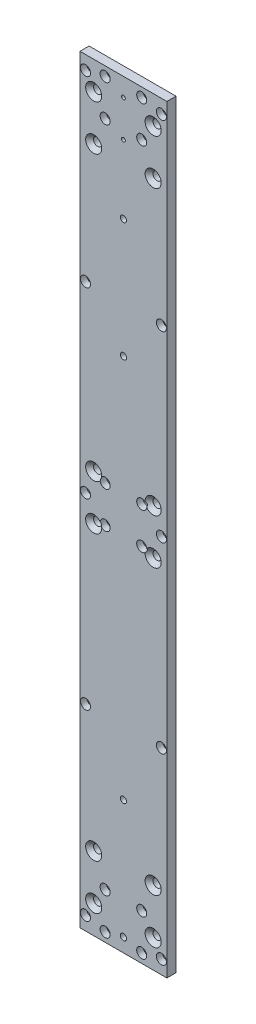
SolidWorks part; units mm, degrees
material "A3钢"
ref_plane "前视基准面" through (0, 0, 0) normal (0, 0, 1) x (1, 0, 0)
ref_plane "上视基准面" through (0, 0, 0) normal (0, 1, 0) x (1, 0, 0)
ref_plane "右视基准面" through (0, 0, 0) normal (1, 0, 0) x (0, 0, -1)
sketch "草图1" plane through (0, 0, 0) normal (0, 0, 1) x (1, 0, 0)
  line L1 (-47.5, -415) -> (47.5, -415)
  line L2 (-47.5, -415) -> (-47.5, 415)
  line L3 (-47.5, 415) -> (47.5, 415)
  line L4 (47.5, -415) -> (47.5, 415)
  line L5 (-47.5, -415) -> (47.5, 415) construction
  line L6 (-47.5, 415) -> (47.5, -415) construction
  point P0 (0, 0)
  dimension "D1" = 95
  dimension "D2" = 830
extrude "凸台-拉伸1" add sketch "草图1" along normal mid plane 10
sketch "草图2" plane through (0, 0, 5) normal (0, 0, 1) x (1, 0, 0)
  line L0 (-154.4275, 0) -> (284.0995, 0) construction
  line L1 (0, 376.6382) -> (0, -407.2879) construction
  line L3 (-20, -405) -> (20, -405)
  line L4 (-20, -405) -> (-20, -365)
  line L5 (-20, -365) -> (20, -365)
  line L6 (20, -405) -> (20, -365)
  line L7 (-20, -405) -> (20, -365) construction
  line L8 (-20, -365) -> (20, -405) construction
  line L9 (-20, -20) -> (20, -20)
  line L10 (-20, -20) -> (-20, 20)
  line L11 (-20, 20) -> (20, 20)
  line L12 (20, -20) -> (20, 20)
  line L13 (-20, -20) -> (20, 20) construction
  line L14 (-20, 20) -> (20, -20) construction
  line L15 (-20, 365) -> (20, 365)
  line L16 (-20, 365) -> (-20, 405)
  line L17 (-20, 405) -> (20, 405)
  line L18 (20, 365) -> (20, 405)
  line L19 (-20, 365) -> (20, 405) construction
  line L20 (-20, 405) -> (20, 365) construction
  point P5 (0, -385)
  point P10 (0, 0)
  point P15 (0, 385)
  dimension "D1" = 40
  dimension "D2" = 770
hole_wizard "打孔尺寸(%根据)内六角圆柱头螺钉的类型1" positions "3D草图1" profile "草图3" counterbore size "M6" standard "GB" end condition through all
sketch3d "3D草图1"
  point P0 (-20, -365, 5)
  point P3 (20, -365, 5)
  point P6 (20, -405, 5)
  point P9 (-20, -405, 5)
  point P13 (-20, 20, 5)
  point P16 (20, 20, 5)
  point P19 (20, -20, 5)
  point P22 (-20, -20, 5)
  point P25 (-20, 405, 5)
  point P28 (20, 405, 5)
  point P31 (20, 365, 5)
  point P34 (-20, 365, 5)
sketch "草图3" plane through (-20, -365, 5) normal (1, 0, 0) x (0, -1, 0)
  line L0 (0, 0) -> (0, 10)
  line L1 (0, 10) -> (3.3, 10)
  line L3 (3.3, 10) -> (3.3, 6.8)
  line L4 (3.3, 6.8) -> (5.5, 6.8)
  line L5 (5.5, 6.8) -> (5.5, 0)
  line L7 (5.5, 0) -> (0, 0)
  line L11 (0, -6.35) -> (0, 107.95) construction
  dimension "通孔孔直径" = 6.6
  dimension "通孔孔深度" = 10
  dimension "柱形沉头孔直径" = 11
  dimension "柱形沉头孔深度" = 6.8
sketch "草图4" plane through (0, 0, 5) normal (0, 0, 1) x (1, 0, 0)
  line L0 (0, -415) -> (0, -400) construction
  line L1 (-47.5, -415) -> (47.5, -415) construction
  line L2 (0, -400) -> (0, -270) construction
  dimension "D1" = 15
  dimension "D2" = 130
hole_wizard "M8 螺纹孔1" positions "3D草图3" profile "草图5" tap size "M8" standard "GB" end condition through all
sketch3d "3D草图3"
  point P0 (0, -400, 5)
  point P3 (0, -270, 5)
sketch "草图5" plane through (0, -400, 5) normal (1, 0, 0) x (0, -1, 0)
  line L0 (0, 0) -> (0, 10)
  line L1 (0, 10) -> (3.4, 10)
  line L2 (3.4, 10) -> (3.4, 0)
  line L5 (3.4, 0) -> (0, 0)
  line L11 (0, -6.35) -> (0, 107.95) construction
  dimension "通孔螺纹孔钻头直径" = 6.8
  dimension "通孔螺纹孔钻头深度" = 10
cosmetic thread "孔螺蚊线1" parameters "D2"=8
cosmetic thread "孔螺蚊线2" parameters "D2"=8
sketch "草图6" plane through (0, 0, 5) normal (0, 0, 1) x (1, 0, 0)
  line L0 (0, 415) -> (0, 280) construction
  line L1 (47.5, 415) -> (-47.5, 415) construction
  line L2 (0, 280) -> (0, 150) construction
  circle A0 centre (0, -270) radius 3.4 construction
  dimension "D1" = 420
  dimension "D2" = 130
hole_wizard "M8 螺纹孔2" positions "3D草图4" profile "草图7" tap size "M8" standard "GB" end condition through all
sketch3d "3D草图4"
  point P0 (0, 280, 5)
  point P3 (0, 150, 5)
sketch "草图7" plane through (0, 280, 5) normal (1, 0, 0) x (0, -1, 0)
  line L0 (0, 0) -> (0, 10)
  line L1 (0, 10) -> (3.4, 10)
  line L2 (3.4, 10) -> (3.4, 0)
  line L5 (3.4, 0) -> (0, 0)
  line L11 (0, -6.35) -> (0, 107.95) construction
  dimension "通孔螺纹孔钻头直径" = 6.8
  dimension "通孔螺纹孔钻头深度" = 10
cosmetic thread "孔螺蚊线3" parameters "D2"=8
cosmetic thread "孔螺蚊线4" parameters "D2"=8
sketch "草图8" plane through (0, 0, 5) normal (0, 0, 1) x (1, 0, 0)
  line L0 (-141.3137, 0) -> (240.7123, 0) construction
  line L1 (41.5, 400) -> (41.5, 200) construction
  line L2 (41.5, 200) -> (41.5, 0) construction
  line L3 (41.5, 0) -> (41.5, -200) construction
  line L4 (41.5, -200) -> (41.5, -400) construction
  line L5 (47.5, -415) -> (47.5, 415) construction
  dimension "D1" = 6
  dimension "D2" = 200
hole_wizard "打孔尺寸(%根据)内六角圆柱头螺钉的类型2" positions "3D草图5" profile "草图9" counterbore size "M6" standard "GB" end condition up to next
sketch3d "3D草图5"
  point P0 (41.5, 400, 5)
  point P3 (41.5, 200, 5)
  point P6 (41.5, 0, 5)
  point P9 (41.5, -200, 5)
  point P12 (41.5, -400, 5)
sketch "草图9" plane through (41.5, 400, 5) normal (1, 0, 0) x (0, -1, 0)
  line L0 (0, 0) -> (0, 10.001)
  line L1 (0, 10.001) -> (3.3, 10.001)
  line L3 (3.3, 10.001) -> (3.3, 6.8)
  line L4 (3.3, 6.8) -> (5.5, 6.8)
  line L5 (5.5, 6.8) -> (5.5, 0)
  line L7 (5.5, 0) -> (0, 0)
  line L11 (0, -6.35) -> (0, 107.95) construction
  dimension "通孔孔直径" = 6.6
  dimension "通孔孔深度" = 10.001
  dimension "柱形沉头孔直径" = 11
  dimension "柱形沉头孔深度" = 6.8
mirror "镜向1" about plane through (0, 0, 0) normal (1, 0, 0) of "打孔尺寸(%根据)内六角圆柱头螺钉的类型2"
sketch "草图10" plane through (0, 0, 5) normal (0, 0, 1) x (1, 0, 0)
  line L0 (0, 395) -> (0, 355) construction
  line L1 (47.5, 415) -> (-47.5, 415) construction
  dimension "D1" = 40
  dimension "D2" = 20
hole_wizard "M5 螺纹孔1" positions "3D草图6" profile "草图11" tap size "M5" standard "GB" end condition through all
sketch3d "3D草图6"
  point P0 (0, 395, 5)
  point P3 (0, 355, 5)
sketch "草图11" plane through (0, 395, 5) normal (1, 0, 0) x (0, -1, 0)
  line L0 (0, 0) -> (0, 10)
  line L1 (0, 10) -> (2.1, 10)
  line L2 (2.1, 10) -> (2.1, 0)
  line L5 (2.1, 0) -> (0, 0)
  line L11 (0, -6.35) -> (0, 107.95) construction
  dimension "通孔螺纹孔钻头直径" = 4.2
  dimension "通孔螺纹孔钻头深度" = 10
cosmetic thread "孔螺蚊线5" parameters "D2"=5
cosmetic thread "孔螺蚊线6" parameters "D2"=5
sketch "草图12" plane through (0, 0, 5) normal (0, 0, 1) x (1, 0, 0)
  line L0 (0, 0) -> (0, 372.8167) construction
  line L1 (-32.5, -24.75) -> (32.5, -24.75)
  line L2 (-32.5, -24.75) -> (-32.5, 24.75)
  line L3 (-32.5, 24.75) -> (32.5, 24.75)
  line L4 (32.5, -24.75) -> (32.5, 24.75)
  line L5 (-32.5, -24.75) -> (32.5, 24.75) construction
  line L6 (-32.5, 24.75) -> (32.5, -24.75) construction
  line L7 (-36, 0) -> (265.8142, 0) construction
  line L8 (-32.5, 334.75) -> (32.5, 334.75)
  line L9 (-32.5, 334.75) -> (-32.5, 384.25)
  line L10 (-32.5, 384.25) -> (32.5, 384.25)
  line L11 (32.5, 334.75) -> (32.5, 384.25)
  line L12 (-32.5, 334.75) -> (32.5, 384.25) construction
  line L13 (-32.5, 384.25) -> (32.5, 334.75) construction
  line L14 (47.5, 415) -> (-47.5, 415) construction
  line L15 (-47.5, -415) -> (47.5, -415) construction
  line L16 (-32.5, -384.25) -> (32.5, -334.75) construction
  line L17 (-32.5, -334.75) -> (32.5, -384.25) construction
  line L18 (32.5, -334.75) -> (32.5, -384.25)
  line L19 (-32.5, -384.25) -> (32.5, -384.25)
  line L20 (-32.5, -334.75) -> (-32.5, -384.25)
  line L21 (-32.5, -334.75) -> (32.5, -334.75)
  circle A0 centre (-41.5, 0) radius 5.5 construction
  point P0 (0, 0)
  point P8 (0, 359.5)
  point P26 (0, -359.5)
  dimension "D1" = 65
  dimension "D2" = 49.5
  dimension "D3" = 65
  dimension "D4" = 49.5
  dimension "D5" = 359.5
hole_wizard "打孔尺寸(%根据)内六角花形半沉头螺钉的类型1" positions "3D草图7" profile "草图13" countersink size "M8" standard "GB" end condition through all
sketch3d "3D草图7"
  point P0 (-32.5, 24.75, 5)
  point P3 (32.5, 24.75, 5)
  point P6 (32.5, -24.75, 5)
  point P9 (-32.5, -24.75, 5)
  point P13 (-32.5, 384.25, 5)
  point P16 (32.5, 384.25, 5)
  point P19 (32.5, 334.75, 5)
  point P22 (-32.5, 334.75, 5)
  point P26 (-32.5, -334.75, 5)
  point P29 (32.5, -334.75, 5)
  point P32 (32.5, -384.25, 5)
  point P35 (-32.5, -384.25, 5)
sketch "草图13" plane through (-32.5, 24.75, 5) normal (1, 0, 0) x (0, -1, 0)
  line L0 (0, 0) -> (0, 10)
  line L1 (0, 10) -> (4.5, 10)
  line L2 (4.5, 10) -> (4.5, 4.3)
  line L3 (4.5, 4.3) -> (8.8, 0)
  line L5 (8.8, 0) -> (0, 0)
  line L6 (-4.5, 4.3) -> (-8.8, 0) construction
  line L11 (0, -6.35) -> (0, 107.95) construction
  dimension "通孔孔直径" = 9
  dimension "通孔孔深度" = 10
  dimension "近端锥形沉头孔直径" = 17.6
  dimension "近端锥形沉头孔角度" = 90
